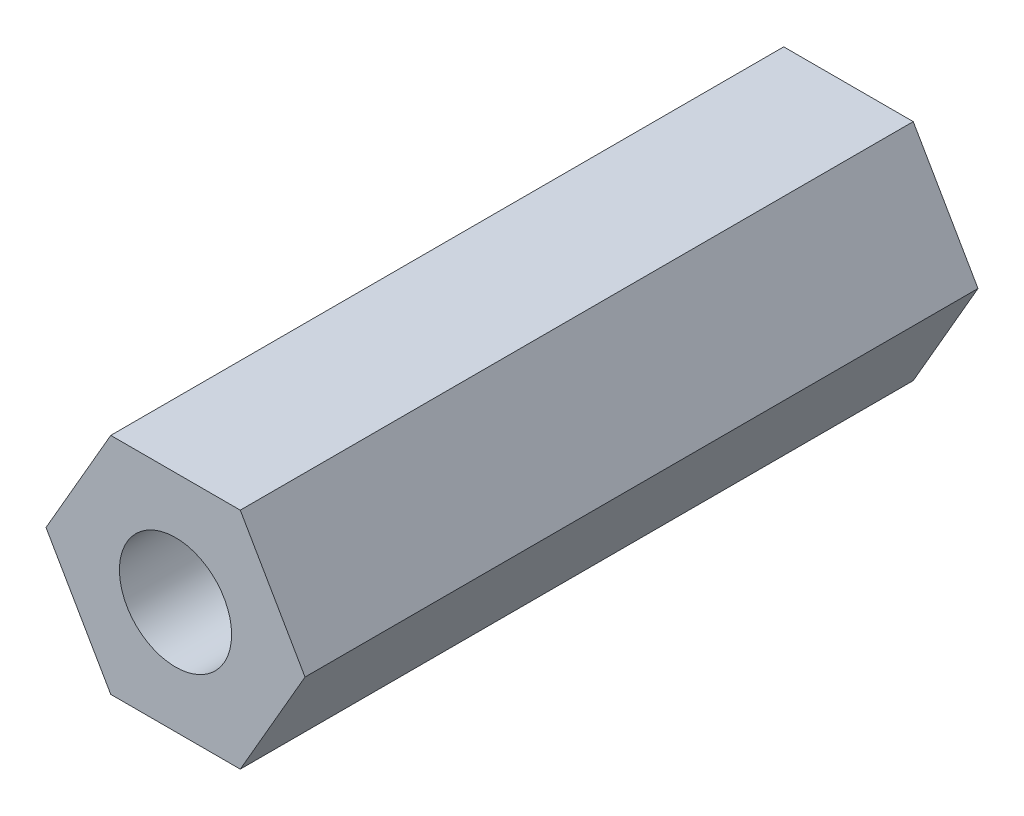
SolidWorks part; units mm, degrees
material "6061 合金"
ref_plane "前视基准面" through (0, 0, 0) normal (0, 0, 1) x (1, 0, 0)
ref_plane "上视基准面" through (0, 0, 0) normal (0, 1, 0) x (1, 0, 0)
ref_plane "右视基准面" through (0, 0, 0) normal (1, 0, 0) x (0, 0, -1)
sketch "草图1" plane through (0, 0, 0) normal (0, 0, 1) x (1, 0, 0)
  line L1 (1.4434, 2.5) -> (-1.4434, 2.5)
  line L2 (-1.4434, 2.5) -> (-2.8868, 0)
  line L3 (-2.8868, 0) -> (-1.4434, -2.5)
  line L4 (-1.4434, -2.5) -> (1.4434, -2.5)
  line L5 (1.4434, -2.5) -> (2.8868, 0)
  line L6 (2.8868, 0) -> (1.4434, 2.5)
  circle A0 centre (0, 0) radius 2.5 construction
  dimension "D1" = 5
extrude "凸台-拉伸1" add sketch "草图1" along normal blind 15
hole_wizard "M3 螺纹孔1" positions "草图2" profile "草图3" tap size "M3" standard "GB" end condition through all
sketch "草图2" plane through (0, 0, 15) normal (0, 0, 1) x (1, 0, 0)
  point P0 (0, 0)
sketch "草图3" plane through (0, 0, 15) normal (1, 0, 0) x (0, -1, 0)
  line L0 (0, 0) -> (0, 15)
  line L1 (0, 15) -> (1.25, 15)
  line L2 (1.25, 15) -> (1.25, 0)
  line L5 (1.25, 0) -> (0, 0)
  line L11 (0, -6.35) -> (0, 107.95) construction
  dimension "通孔螺纹孔钻头直径" = 2.5
  dimension "通孔螺纹孔钻头深度" = 15
cosmetic thread "孔螺蚊线1"
